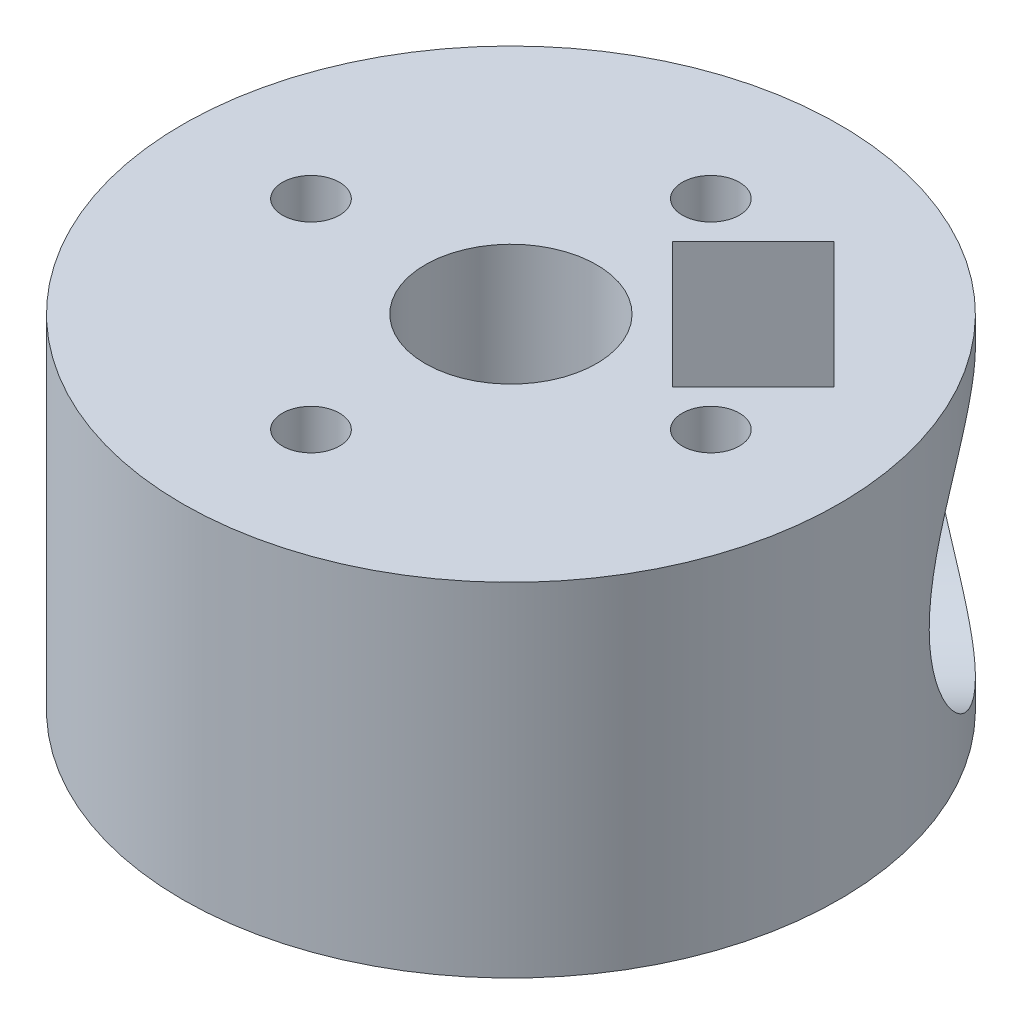
SolidWorks part; units mm, degrees
ref_plane "Alzado" through (0, 0, 0) normal (0, 0, 1) x (1, 0, 0)
ref_plane "Planta" through (0, 0, 0) normal (0, 1, 0) x (1, 0, 0)
ref_plane "Vista lateral" through (0, 0, 0) normal (1, 0, 0) x (0, 0, -1)
sketch "Croquis1" plane through (0, 0, 0) normal (0, 1, 0) x (1, 0, 0)
  line L0 (0, 11.5) -> (0, -11.5) construction
  circle A0 centre (0, 0) radius 11.5
  circle A1 centre (0, 0) radius 3
  circle A2 centre (0, 7) radius 1
  circle A3 centre (7, 0) radius 1
  circle A4 centre (0, -7) radius 1
  circle A5 centre (-7, 0) radius 1
  point P17 (0, 0)
  dimension "D1" = 23
  dimension "D2" = 6
  dimension "D4" = 2
  dimension "D3" = 7
  dimension "D5" = 4
extrude "Saliente-Extruir1" add sketch "Croquis1" along normal blind 12
sketch "Croquis2" plane through (0, 12, 0) normal (0, 1, 0) x (1, 0, 0)
  line L0 (0, 0) -> (11.5, 0) construction
  line L1 (0, 0) -> (8.1317, 8.1317) construction
  line L2 (5.6569, 5.6569) -> (2.8284, 2.8284)
  line L3 (5.6569, 5.6569) -> (3.4471, 7.8666)
  line L4 (2.8284, 2.8284) -> (0.6187, 5.0381)
  line L5 (3.4471, 7.8666) -> (0.6187, 5.0381)
  line L6 (5.6569, 5.6569) -> (2.8284, 2.8284)
  line L7 (5.6569, 5.6569) -> (7.8666, 3.4471)
  line L8 (2.8284, 2.8284) -> (5.0381, 0.6187)
  line L9 (7.8666, 3.4471) -> (5.0381, 0.6187)
  circle A0 centre (0, 0) radius 11.5 construction
  dimension "D1" = 45
  dimension "D2" = 3.125
  dimension "D3" = 3.125
  dimension "D4" = 4
  dimension "D5" = 4
extrude "Cortar-Extruir1" cut sketch "Croquis2" against normal through all contours L9 L7 L2 L8 | L3 L5 L4 L2
sketch "Croquis3" plane through (2.8284, 0, -2.8284) normal (0.7071, 0, -0.7071) x (-0.7071, 0, -0.7071)
  line L0 (0, 12) -> (0, 0) construction
  line L1 (3.125, 12) -> (-3.125, 12) construction
  line L2 (0, 6) -> (-11.5, 6) construction
  line L3 (-11.5, 12) -> (-11.5, 0) construction
  line L4 (-11.5, 6) -> (11.5, 6) construction
  line L5 (11.5, 0) -> (11.5, 12) construction
  circle A0 centre (0, 6) radius 1.5
  dimension "D1" = 3
extrude "Cortar-Extruir2" cut sketch "Croquis3" against normal blind 12 from offset 10
sketch "Croquis4" plane through (2.8284, 0, -2.8284) normal (0.7071, 0, -0.7071) x (-0.7071, 0, -0.7071)
  circle A0 centre (0, 6) radius 5
  dimension "D1" = 10
extrude "Cortar-Extruir3" cut sketch "Croquis4" against normal blind 4 from offset 10
